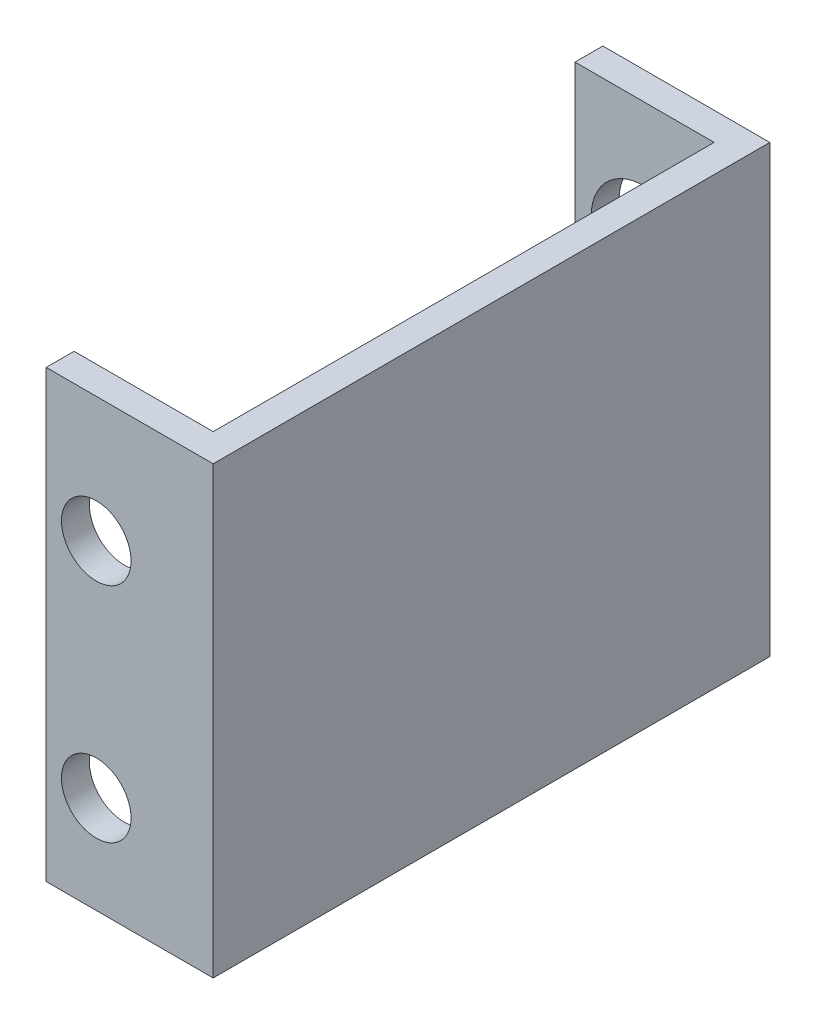
SolidWorks part; units mm, degrees
ref_plane "Front Plane" through (0, 0, 0) normal (0, 0, 1) x (1, 0, 0)
ref_plane "Top Plane" through (0, 0, 0) normal (0, 1, 0) x (1, 0, 0)
ref_plane "Right Plane" through (0, 0, 0) normal (1, 0, 0) x (0, 0, -1)
sketch "Sketch1" plane through (0, 0, 0) normal (0, 1, 0) x (1, 0, 0)
  line L0 (-19.05, 63.5) -> (-19.05, 60.325)
  line L1 (-19.05, 63.5) -> (0, 63.5)
  line L2 (0, 63.5) -> (0, 0)
  line L6 (-3.175, 3.18) -> (-3.175, 60.325)
  line L7 (-3.175, 60.325) -> (-19.05, 60.325)
  line L11 (0, 0) -> (-19.05, 0)
  line L12 (-19.05, 0) -> (-19.05, 3.18)
  line L13 (-19.05, 3.18) -> (-3.175, 3.18)
  dimension "D1" = 63.5
  dimension "D2" = 3.18
  dimension "D3" = 3.175
  dimension "D4" = 3.175
  dimension "D5" = 19.05
  dimension "D6" = 19.05
extrude "Boss-Extrude3" add sketch "Sketch1" along normal blind 50.8
sketch "Sketch8" plane through (0, 0, -63.5) normal (0, 0, -1) x (-1, 0, 0)
  line L1 (19.05, 50.8) -> (19.05, 0) construction
  line L2 (0, 0) -> (19.05, 0) construction
  circle A0 centre (11.2, 36.5125) radius 6
  dimension "D3" = 12
  dimension "D1" = 7.85
  dimension "D2" = 36.5125
extrude "Panel Mount Hole" cut sketch "Sketch8" against normal blind 4
sketch "Sketch9" plane through (0, 0, -3.18) normal (0, 0, -1) x (-1, 0, 0)
  line L0 (19.05, 50.8) -> (3.175, 50.8) construction
  line L1 (3.175, 50.8) -> (3.175, 0) construction
  line L2 (3.175, 0) -> (19.05, 0) construction
  line L3 (19.05, 0) -> (19.05, 50.8) construction
  line L4 (13.335, 0) -> (13.335, 50.8) construction
  circle A0 centre (13.335, 36.5125) radius 3.9688
  circle A1 centre (13.335, 11.1125) radius 3.9688
  dimension "D4" = 7.9375
  dimension "D5" = 7.9375
  dimension "D1" = 10.16
  dimension "D2" = 14.2875
  dimension "D3" = 25.4
extrude "Cut-Extrude1" cut sketch "Sketch9" against normal up to next
